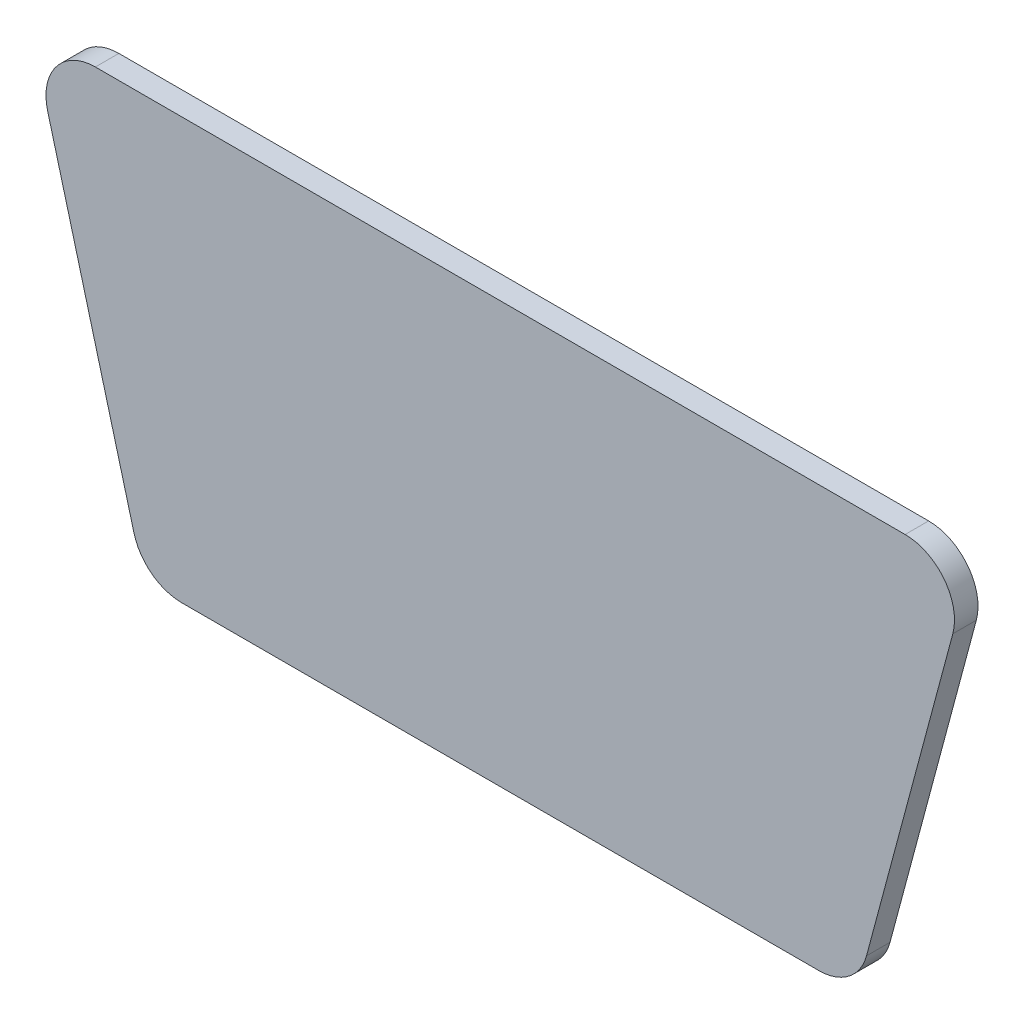
SolidWorks part; units mm, degrees
ref_plane "Front Plane" through (0, 0, 0) normal (0, 0, 1) x (1, 0, 0)
ref_plane "Top Plane" through (0, 0, 0) normal (0, 1, 0) x (1, 0, 0)
ref_plane "Right Plane" through (0, 0, 0) normal (1, 0, 0) x (0, 0, -1)
sketch "Sketch1" plane through (0, 0, 0) normal (0, 0, 1) x (1, 0, 0)
  line L0 (-135.2667, 0) -> (178.1738, 0) construction
  line L1 (0, 93.814) -> (0, -102.1772) construction
  line L2 (-10.0599, 3.0368) -> (-8.2244, -3.8132) construction
  line L3 (-13.95, 6.25) -> (13.95, 6.25) construction
  line L4 (-15.45, 4.75) -> (-15.45, -4.75) construction
  line L5 (-13.95, -6.25) -> (13.95, -6.25) construction
  line L6 (15.45, 4.75) -> (15.45, -4.75) construction
  line L7 (-15.45, 6.25) -> (15.45, -6.25) construction
  line L8 (-15.45, -6.25) -> (15.45, 6.25) construction
  line L9 (-8.611, 4.925) -> (8.611, 4.925) construction
  line L10 (10.0599, 3.0368) -> (8.2244, -3.8132) construction
  line L11 (-6.7756, -4.925) -> (6.7756, -4.925) construction
  line L12 (-8.611, 4.175) -> (8.611, 4.175) construction
  line L13 (-8.25, 4) -> (8.25, -4) construction
  line L14 (-8.25, -4) -> (8.25, 4) construction
  line L15 (9.3355, 3.2309) -> (7.5, -3.6191) construction
  line L16 (-6.7756, -4.175) -> (6.7756, -4.175) construction
  line L17 (-9.3355, 3.2309) -> (-7.5, -3.6191) construction
  line L18 (-8.611, 4.475) -> (8.611, 4.475)
  line L19 (9.6252, 3.1532) -> (7.7898, -3.6968)
  line L20 (-6.7756, -4.475) -> (6.7756, -4.475)
  line L21 (-9.6252, 3.1532) -> (-7.7898, -3.6968)
  circle A0 centre (-12.5, 0) radius 1.55 construction
  circle A1 centre (12.5, 0) radius 1.55 construction
  arc A2 (10.0599, 3.0368) -> (8.611, 4.925) centre (8.611, 3.425) ccw construction
  arc A3 (-10.0599, 3.0368) -> (-8.611, 4.925) centre (-8.611, 3.425) cw construction
  arc A4 (6.7756, -4.925) -> (8.2244, -3.8132) centre (6.7756, -3.425) ccw construction
  arc A5 (-8.2244, -3.8132) -> (-6.7756, -4.925) centre (-6.7756, -3.425) ccw construction
  arc A6 (13.95, 6.25) -> (15.45, 4.75) centre (13.95, 4.75) cw construction
  arc A7 (13.95, -6.25) -> (15.45, -4.75) centre (13.95, -4.75) ccw construction
  arc A8 (-15.45, -4.75) -> (-13.95, -6.25) centre (-13.95, -4.75) ccw construction
  arc A9 (-13.95, 6.25) -> (-15.45, 4.75) centre (-13.95, 4.75) ccw construction
  arc A10 (9.3355, 3.2309) -> (8.611, 4.175) centre (8.611, 3.425) ccw construction
  arc A11 (6.7756, -4.175) -> (7.5, -3.6191) centre (6.7756, -3.425) ccw construction
  arc A12 (-7.5, -3.6191) -> (-6.7756, -4.175) centre (-6.7756, -3.425) ccw construction
  arc A13 (-9.3355, 3.2309) -> (-8.611, 4.175) centre (-8.611, 3.425) cw construction
  arc A14 (9.6252, 3.1532) -> (8.611, 4.475) centre (8.611, 3.425) ccw
  arc A15 (6.7756, -4.475) -> (7.7898, -3.6968) centre (6.7756, -3.425) ccw
  arc A16 (-7.7898, -3.6968) -> (-6.7756, -4.475) centre (-6.7756, -3.425) ccw
  arc A17 (-9.6252, 3.1532) -> (-8.611, 4.475) centre (-8.611, 3.425) cw
  point P5 (0, 0)
  point P14 (0, 0)
  dimension "D1" = 16.5
  dimension "D6" = 1.5
  dimension "D7" = 1.5
  dimension "D2" = 1.5
  dimension "D8" = 3.1
  dimension "D3" = 30.9
  dimension "D4" = 12.5
  dimension "D5" = 12.5
  dimension "D10" = 8.35
  dimension "D11" = 105
  dimension "D12" = 105
  dimension "D13" = 15
  dimension "D9" = 0.75
  dimension "D14" = 0.3
extrude "Boss-Extrude1" add sketch "Sketch1" along normal blind 0.5 contours L21 A16 L20 A15 L19 A14 L18 A17
